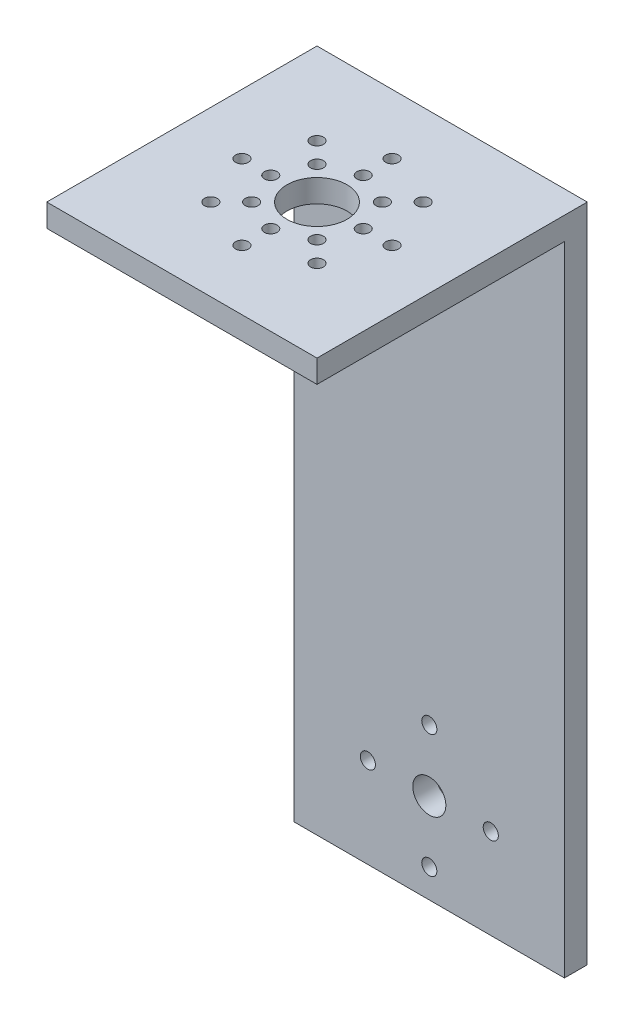
SolidWorks part; units mm, degrees
ref_plane "Front Plane" through (0, 0, 0) normal (0, 0, 1) x (1, 0, 0)
ref_plane "Top Plane" through (0, 0, 0) normal (0, 1, 0) x (1, 0, 0)
ref_plane "Right Plane" through (0, 0, 0) normal (1, 0, 0) x (0, 0, -1)
sketch "Sketch1" plane through (0, 0, 0) normal (1, 0, 0) x (0, 0, -1)
  line L0 (0, 0) -> (57.15, 0)
  line L1 (57.15, 0) -> (57.15, -139.7)
  dimension "D1" = 57.15
  dimension "D2" = 139.7
extrude "Extrude-Thin1" add sketch "Sketch1" along normal blind 57.15 thin
sketch "Sketch2" plane through (0, 0, 0) normal (0, 1, 0) x (1, 0, 0)
  line L0 (0, 0) -> (57.15, 57.15) construction
  line L1 (0, 57.15) -> (57.15, 0) construction
  circle A0 centre (28.575, 28.575) radius 15.875 construction
  circle A1 centre (28.575, 28.575) radius 9.779 construction
  circle A3 centre (28.575, 28.575) radius 6.35
  point P11 (21.6602, 35.4898)
  point P12 (17.3497, 39.8003)
  dimension "D1" = 31.75
  dimension "D2" = 19.558
  dimension "D3" = 12.7
hole_wizard "M2.5 Clearance Hole1" positions "Sketch3" profile "Sketch4" hole size "M2.5" standard "ANSI Metric"
sketch "Sketch3" plane through (0, 0, 0) normal (0, 1, 0) x (1, 0, 0)
  point P0 (17.3497, 39.8003)
  point P3 (21.6602, 35.4898)
sketch "Sketch4" plane through (17.3497, 0, -39.8003) normal (1, 0, 0) x (0, 0, 1)
  line L0 (0, 0) -> (0, 5.8927)
  line L1 (0, 5.8927) -> (1.3525, 5.08)
  line L2 (1.3525, 5.08) -> (1.3525, 0)
  line L5 (1.3525, 0) -> (0, 0)
  line L10 (0, 5.8927) -> (-1.3525, 5.08) construction
  line L11 (0, -6.35) -> (0, 107.95) construction
  dimension "Hole Dia." = 2.7051
  dimension "Hole Depth" = 5.08
  dimension "Drill Angle" = 118
extrude "Cut-Extrude1" cut sketch "Sketch2" against normal up to next
pattern_circular "CirPattern1" count 8 over 360 about axis through (28.575, 0, -28.575) along (0, 1, 0) of "M2.5 Clearance Hole1"
sketch "Sketch5" plane through (0, 0, -57.15) normal (0, 0, -1) x (-1, 0, 0)
  line L0 (-57.15, -19.05) -> (0, -19.05) construction
  line L1 (-57.15, 0) -> (-57.15, -139.7) construction
  line L2 (0, 0) -> (0, -139.7) construction
  line L3 (-57.15, 0) -> (0, 0) construction
  line L4 (-57.15, -120.65) -> (0, -120.65) construction
  circle A0 centre (-28.575, -120.65) radius 3.5
  circle A1 centre (-28.575, -120.65) radius 13 construction
  point P13 (-28.575, -107.65)
  point P14 (-41.575, -120.65)
  point P15 (0, 0)
  dimension "D3" = 7
  dimension "D4" = 26
  dimension "D1" = 19.05
  dimension "D2" = 101.6
extrude "Cut-Extrude2" cut sketch "Sketch5" against normal up to next
hole_wizard "M3 Clearance Hole1" positions "Sketch6" profile "Sketch7" hole size "M3" standard "ANSI Metric"
sketch "Sketch6" plane through (0, 0, -57.15) normal (0, 0, -1) x (-1, 0, 0)
  point P0 (-28.575, -107.65)
sketch "Sketch7" plane through (28.575, -107.65, -57.15) normal (1, 0, 0) x (0, 1, 0)
  line L0 (0, 0) -> (0, 6.0414)
  line L1 (0, 6.0414) -> (1.6, 5.08)
  line L2 (1.6, 5.08) -> (1.6, 0)
  line L5 (1.6, 0) -> (0, 0)
  line L10 (0, 6.0414) -> (-1.6, 5.08) construction
  line L11 (0, -6.35) -> (0, 107.95) construction
  dimension "Hole Dia." = 3.2
  dimension "Hole Depth" = 5.08
  dimension "Drill Angle" = 118
pattern_circular "CirPattern2" count 4 over 360 about axis through (28.575, -120.65, 0) along (0, 0, 1) of "M3 Clearance Hole1"
